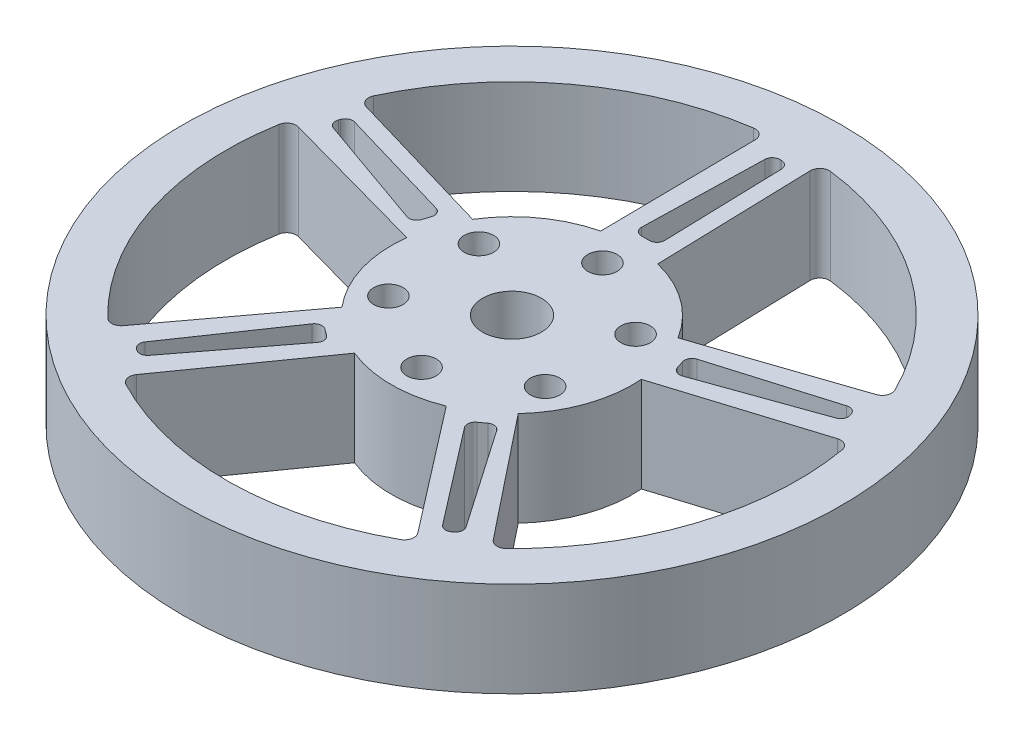
SolidWorks part; units mm, degrees
ref_plane "Front Plane" through (0, 0, 0) normal (0, 0, 1) x (1, 0, 0)
ref_plane "Top Plane" through (0, 0, 0) normal (0, 1, 0) x (1, 0, 0)
ref_plane "Right Plane" through (0, 0, 0) normal (1, 0, 0) x (0, 0, -1)
sketch "Sketch1" plane through (0, 0, 0) normal (0, 1, 0) x (1, 0, 0)
  line L0 (0, -6.6294) -> (0, -16.1544) construction
  line L1 (0, -6.6294) -> (8.2489, -11.3919) construction
  line L2 (0, -6.6294) -> (8.2489, -1.8669) construction
  line L3 (0, -6.6294) -> (0, 33.015) construction
  line L4 (0, -6.6294) -> (37.7041, 5.6214) construction
  line L5 (0, -6.6294) -> (23.3024, -38.7024) construction
  line L6 (0, -6.6294) -> (-23.3024, -38.7024) construction
  line L7 (0, -6.6294) -> (-37.7041, 5.6214) construction
  line L8 (-2.5, 23.3666) -> (2.5, 23.3666) construction
  line L9 (-3, 5.7112) -> (3, 5.7112) construction
  line L10 (-3.2021, 23.2998) -> (-3, 5.7112)
  line L11 (2.5, 23.3666) -> (3, 5.7112)
  line L12 (-0.8753, 21.6666) -> (0.8475, 21.6666)
  line L13 (0.8475, 21.6666) -> (1.2512, 7.4112)
  line L14 (1.2512, 7.4112) -> (-1.2212, 7.4112)
  line L15 (-1.2212, 7.4112) -> (-0.8753, 21.6666)
  line L16 (27.4748, 5.6647) -> (10.8095, 0.0373)
  line L17 (12.976, -1.1292) -> (26.6406, 2.9471)
  line L18 (27.173, 1.3086) -> (13.74, -3.4805)
  line L19 (26.6406, 2.9471) -> (27.173, 1.3086)
  line L20 (13.74, -3.4805) -> (12.976, -1.1292)
  line L21 (29.4539, -0.4261) -> (12.6636, -5.6691)
  line L22 (20.1825, -28.9604) -> (9.3004, -15.2776)
  line L23 (9.2408, -17.2706) -> (17.3401, -29.0068)
  line L24 (15.9464, -30.0194) -> (7.2406, -18.7238)
  line L25 (17.3401, -29.0068) -> (15.9464, -30.0194)
  line L26 (7.2406, -18.7238) -> (9.2408, -17.2706)
  line L27 (15.6087, -32.3661) -> (4.8266, -18.3765)
  line L28 (-15.0014, -32.7247) -> (-4.8266, -18.3765)
  line L29 (-7.2649, -18.7062) -> (-15.9238, -30.0358)
  line L30 (-17.3176, -29.0232) -> (-9.2651, -17.253)
  line L31 (-15.9238, -30.0358) -> (-17.3176, -29.0232)
  line L32 (-9.2651, -17.253) -> (-7.2649, -18.7062)
  line L33 (-20.1825, -28.9604) -> (-9.6807, -14.8497)
  line L34 (-29.4539, -0.4261) -> (-12.6075, -5.0994)
  line L35 (-13.7307, -3.452) -> (-27.1816, 1.2821)
  line L36 (-26.6492, 2.9206) -> (-12.9668, -1.1006)
  line L37 (-27.1816, 1.2821) -> (-26.6492, 2.9206)
  line L38 (-12.9668, -1.1006) -> (-13.7307, -3.452)
  line L39 (-27.7553, 5.0176) -> (-10.8095, 0.0373)
  line L40 (0, -6.6294) -> (-8.2489, -11.3919) construction
  line L41 (0, -6.6294) -> (-8.2489, -1.8669) construction
  circle A0 centre (0, -6.6294) radius 12.7 construction
  circle A1 centre (0, 2.8956) radius 1.55
  circle A2 centre (-8.2489, -1.8669) radius 1.55
  circle A3 centre (-8.2489, -11.3919) radius 1.55
  circle A4 centre (0, -16.1544) radius 1.55
  circle A5 centre (0, -6.6294) radius 34.7
  circle A6 centre (8.2489, -1.8669) radius 1.55
  circle A7 centre (0, -6.6294) radius 3.1
  circle A8 centre (8.2489, -11.3919) radius 1.55
  circle A9 centre (0, -6.6294) radius 30.1 construction
  arc A10 (-3, 5.7112) -> (-10.8095, 0.0373) centre (0, -6.6294) ccw
  arc A11 (10.8095, 0.0373) -> (3, 5.7112) centre (0, -6.6294) ccw
  arc A12 (9.3004, -15.2776) -> (12.6636, -5.6691) centre (0, -6.6294) ccw
  arc A13 (4.8266, -18.3765) -> (-4.8266, -18.3765) centre (0, -6.6294) cw
  arc A14 (-12.6075, -5.0994) -> (-9.6807, -14.8497) centre (0, -6.6294) ccw
  arc A15 (-27.7553, 5.0176) -> (-3.2021, 23.2998) centre (0, -6.6294) cw
  arc A16 (2.5, 23.3666) -> (27.4748, 5.6647) centre (0, -6.6294) cw
  arc A17 (29.4539, -0.4261) -> (20.1825, -28.9604) centre (0, -6.6294) cw
  arc A18 (15.6087, -32.3661) -> (-15.0014, -32.7247) centre (0, -6.6294) cw
  arc A19 (-20.1825, -28.9604) -> (-29.4539, -0.4261) centre (0, -6.6294) cw
  point P25 (0, -6.6294)
  point P66 (0, -6.6294)
  dimension "D1" = 3.1
  dimension "D2" = 3.1
  dimension "D5" = 69.4
  dimension "D6" = 60.2
  dimension "D9" = 25.4
  dimension "D16" = 6.2
  dimension "D17" = 3.1
  dimension "D18" = 3.1
  dimension "D19" = 3.1
  dimension "D20" = 3.1
  dimension "D21" = 9.525
  dimension "D28" = 30.1
  dimension "D29" = 30.1
  dimension "D30" = 12.7
  dimension "D31" = 12.7
  dimension "D3" = 60
  dimension "D4" = 60
  dimension "D8" = 2.5
  dimension "D10" = 3
  dimension "D11" = 1.7
  dimension "D12" = 9.525
  dimension "D13" = 1.7
  dimension "D14" = 1.7
  dimension "D22" = 9.525
  dimension "D23" = 9.525
  dimension "D24" = 9.525
  dimension "D25" = 9.525
  dimension "D26" = 60
  dimension "D27" = 60
  dimension "D7" = 5
  dimension "D15" = 5
extrude "Boss-Extrude1" add sketch "Sketch1" along normal blind 10
fillet "Fillet2" radius 1 10 edges at (-20.1825, 5, 28.9604) (-15.0014, 5, 32.7247) (15.6087, 5, 32.3661) (20.1825, 5, 28.9604) (29.4539, 5, 0.4261) (27.4748, 5, -5.6647) (2.5, 5, -23.3666) (-3.2021, 5, -23.2998) (-29.4539, 5, 0.4261) (-27.7553, 5, -5.0176)
fillet "Fillet3" radius 0.8 20 edges at (-27.1816, 5, -1.2821) (-26.6492, 5, -2.9206) (-12.9668, 5, 1.1006) (-13.7307, 5, 3.452) (-15.9238, 5, 30.0358) (-17.3176, 5, 29.0232) (-9.2651, 5, 17.253) (-7.2649, 5, 18.7062) (17.3401, 5, 29.0068) (15.9464, 5, 30.0194) (7.2406, 5, 18.7238) (9.2408, 5, 17.2706) (12.976, 5, 1.1292) (26.6406, 5, -2.9471) (27.173, 5, -1.3086) (13.74, 5, 3.4805) (-0.8753, 5, -21.6666) (0.8475, 5, -21.6666) (-1.2212, 5, -7.4112) (1.2512, 5, -7.4112)
